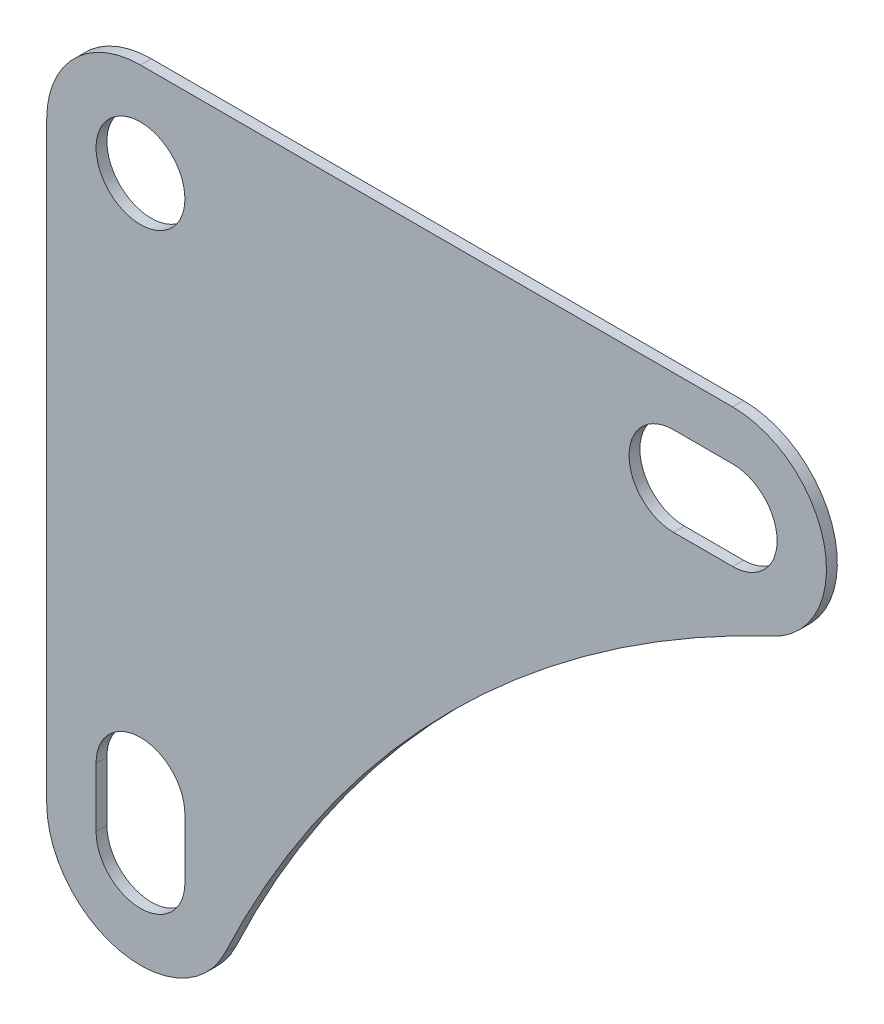
SolidWorks part; units mm, degrees
ref_plane "Front Plane" through (0, 0, 0) normal (0, 0, 1) x (1, 0, 0)
ref_plane "Top Plane" through (0, 0, 0) normal (0, 1, 0) x (1, 0, 0)
ref_plane "Right Plane" through (0, 0, 0) normal (1, 0, 0) x (0, 0, -1)
sketch "Sketch1" plane through (0, 0, 0) normal (0, 0, 1) x (1, 0, 0)
  line L0 (-9.5, -60) -> (-9.5, 0)
  line L1 (0, 9.5) -> (60, 9.5)
  line L3 (0, -60) -> (0, -54) construction
  line L4 (-4.5, -60) -> (-4.5, -54)
  line L5 (4.5, -60) -> (4.5, -54)
  line L6 (60, 0) -> (54, 0) construction
  line L7 (60, -4.5) -> (54, -4.5)
  line L8 (60, 4.5) -> (54, 4.5)
  arc A0 (-9.5, 0) -> (0, 9.5) centre (0, 0) cw
  arc A1 (60, 9.5) -> (64.0363, -8.5999) centre (60, 0) cw
  arc A2 (8.5999, -64.0363) -> (-9.5, -60) centre (0, -60) cw
  circle A3 centre (0, 0) radius 4.5
  arc A4 (-4.5, -60) -> (4.5, -60) centre (0, -60) ccw
  arc A5 (4.5, -54) -> (-4.5, -54) centre (0, -54) ccw
  arc A6 (60, -4.5) -> (60, 4.5) centre (60, 0) ccw
  arc A7 (54, 4.5) -> (54, -4.5) centre (54, 0) ccw
  arc A8 (8.5999, -64.0363) -> (64.0363, -8.5999) centre (113.068, -113.068) cw
  point P11 (0, -57)
  point P17 (57, 0)
  dimension "D7" = 9
  dimension "D1" = 79
  dimension "D2" = 79
  dimension "D3" = 54
  dimension "D4" = 5
  dimension "D5" = 5
  dimension "D6" = 5
  dimension "D8" = 15
  dimension "D9" = 15
extrude "Boss-Extrude1" add sketch "Sketch1" against normal blind 1.1
equation "\"D1@Sketch1\"=\"D2@Sketch1\""
